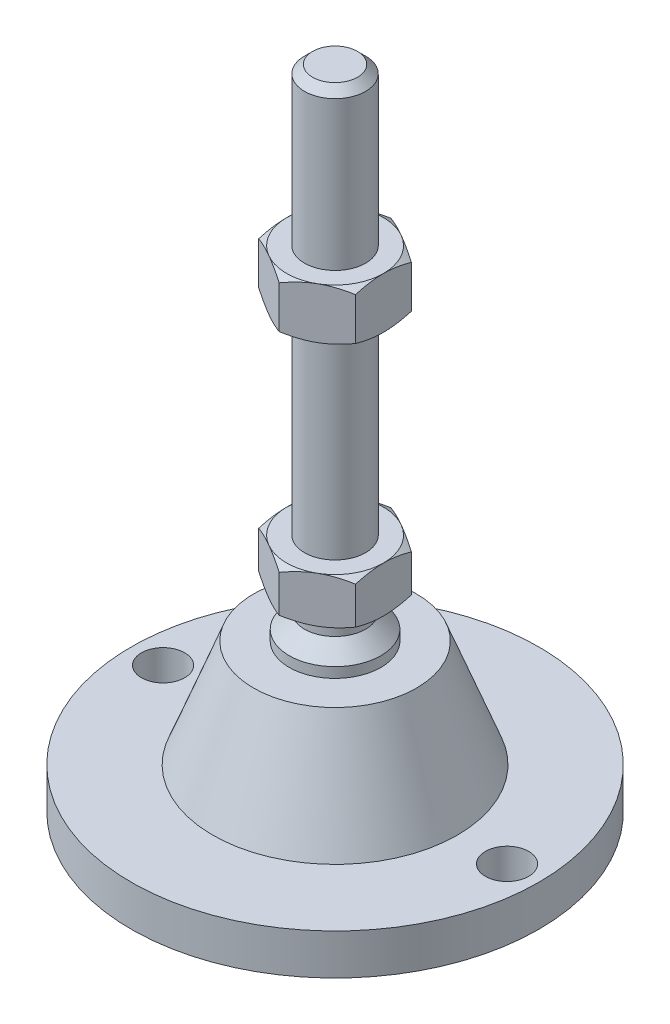
SolidWorks part; units mm, degrees
ref_plane "Спереди" through (0, 0, 0) normal (0, 0, 1) x (1, 0, 0)
ref_plane "Сверху" through (0, 0, 0) normal (0, 1, 0) x (1, 0, 0)
ref_plane "Справа" through (0, 0, 0) normal (1, 0, 0) x (0, 0, -1)
sketch "Эскиз1" plane through (0, 0, 0) normal (0, 0, 1) x (1, 0, 0)
  line L0 (0, 0) -> (-40, 0)
  line L3 (-40, 0) -> (-40, 8)
  line L12 (-6, 47) -> (-6, 125.4)
  line L13 (-6, 125.4) -> (-4.4, 127)
  line L14 (-4.4, 127) -> (0, 127)
  line L15 (0, 127) -> (0, 0) construction
  line L16 (-40, 8) -> (-24, 8)
  line L17 (0, 0) -> (0, 127)
  line L18 (0, 0) -> (0, -7.9595) construction
  line L19 (-6, 47) -> (-6, 38)
  line L21 (-9, 29) -> (-16, 29)
  line L22 (-24, 8) -> (-16, 29)
  line L23 (-9, 29) -> (-9, 31)
  line L24 (-9, 31) -> (-6, 34)
  line L25 (-6, 34) -> (-6, 38)
  line L26 (-6, 47) -> (0, 47) construction
  point P8 (-6, 86.2)
revolve "Повернуть1" add sketch "Эскиз1" angle 360 about L17
ref_plane "Плоскость2" through (0, 38, 0) normal (0, 1, 0) x (1, 0, 0)
sketch "Эскиз2" plane through (0, 38, 0) normal (0, 1, 0) x (1, 0, 0)
  line L1 (0, 10.9697) -> (-9.5, 5.4848)
  line L2 (-9.5, 5.4848) -> (-9.5, -5.4848)
  line L3 (-9.5, -5.4848) -> (0, -10.9697)
  line L4 (0, -10.9697) -> (9.5, -5.4848)
  line L5 (9.5, -5.4848) -> (9.5, 5.4848)
  line L6 (9.5, 5.4848) -> (0, 10.9697)
  circle A0 centre (0, 0) radius 9.5 construction
  dimension "D1" = 19
extrude "Бобышка-Вытянуть1" add sketch "Эскиз2" along normal up to vertex (9 mm away) up to point (-6, 47, 0)
ref_plane "Плоскость1" through (0, 86.2, 0) normal (0, 1, 0) x (1, 0, 0)
sketch "Эскиз3" plane through (0, 86.2, 0) normal (0, 1, 0) x (1, 0, 0)
  line L6 (9.5, 5.4848) -> (0, 10.9697)
  line L7 (0, 10.9697) -> (-9.5, 5.4848)
  line L8 (-9.5, 5.4848) -> (-9.5, -5.4848)
  line L9 (-9.5, -5.4848) -> (0, -10.9697)
  line L10 (0, -10.9697) -> (9.5, -5.4848)
  line L11 (9.5, -5.4848) -> (9.5, 5.4848)
  line L12 (9.5, 5.4848) -> (0, 10.9697)
  line L13 (0, 10.9697) -> (-9.5, 5.4848)
  line L14 (-9.5, 5.4848) -> (-9.5, -5.4848)
  line L15 (-9.5, -5.4848) -> (0, -10.9697)
  line L16 (0, -10.9697) -> (9.5, -5.4848)
  line L17 (9.5, -5.4848) -> (9.5, 5.4848)
  dimension "D1" = 0
extrude "Бобышка-Вытянуть2" add sketch "Эскиз3" along normal blind 10
sketch "Эскиз4" plane through (0, 0, 0) normal (0, 0, 1) x (1, 0, 0)
  line L0 (-9.5, 96.2) -> (-18.1603, 91.2)
  line L1 (-18.1603, 91.2) -> (-18.1603, 96.2)
  line L2 (-18.1603, 96.2) -> (-9.5, 96.2)
  line L3 (-18.1603, 91.2) -> (-9.5, 86.2)
  line L4 (50, 86.2) -> (-50, 86.2) construction
  line L5 (-9.5, 86.2) -> (-18.1603, 86.2)
  line L6 (-18.1603, 86.2) -> (-18.1603, 91.2)
  line L7 (-9.5, 96.2) -> (-9.5, 86.2) construction
  line L8 (-9.5, 47) -> (-17.2942, 47)
  line L9 (-17.2942, 47) -> (-17.2942, 42.5)
  line L10 (-17.2942, 42.5) -> (-9.5, 47)
  line L11 (-9.5, 38) -> (-17.2942, 42.5)
  line L12 (-17.2942, 42.5) -> (-17.2942, 38)
  line L13 (-17.2942, 38) -> (-9.5, 38)
  line L14 (0, 127) -> (0, 96.3793) construction
  line L15 (50, 38) -> (-50, 38) construction
  dimension "D1" = 30
  dimension "D2" = 30
revolve "Вырез-Повернуть2" cut sketch "Эскиз4" angle 360 about L14
sketch "Эскиз5" plane through (0, 8, 0) normal (0, 1, 0) x (1, 0, 0)
  line L0 (33.75, 0) -> (-33.75, 0) construction
  circle A0 centre (-33.75, 0) radius 4.25
  circle A1 centre (33.75, 0) radius 4.25
  circle A2 centre (0, 0) radius 40 construction
  dimension "D1" = 8.5
  dimension "D2" = 2
extrude "Вырез-Вытянуть1" cut sketch "Эскиз5" against normal through all
equation "\"D13@Эскиз1\"=\"D12@Эскиз1\"/2"
